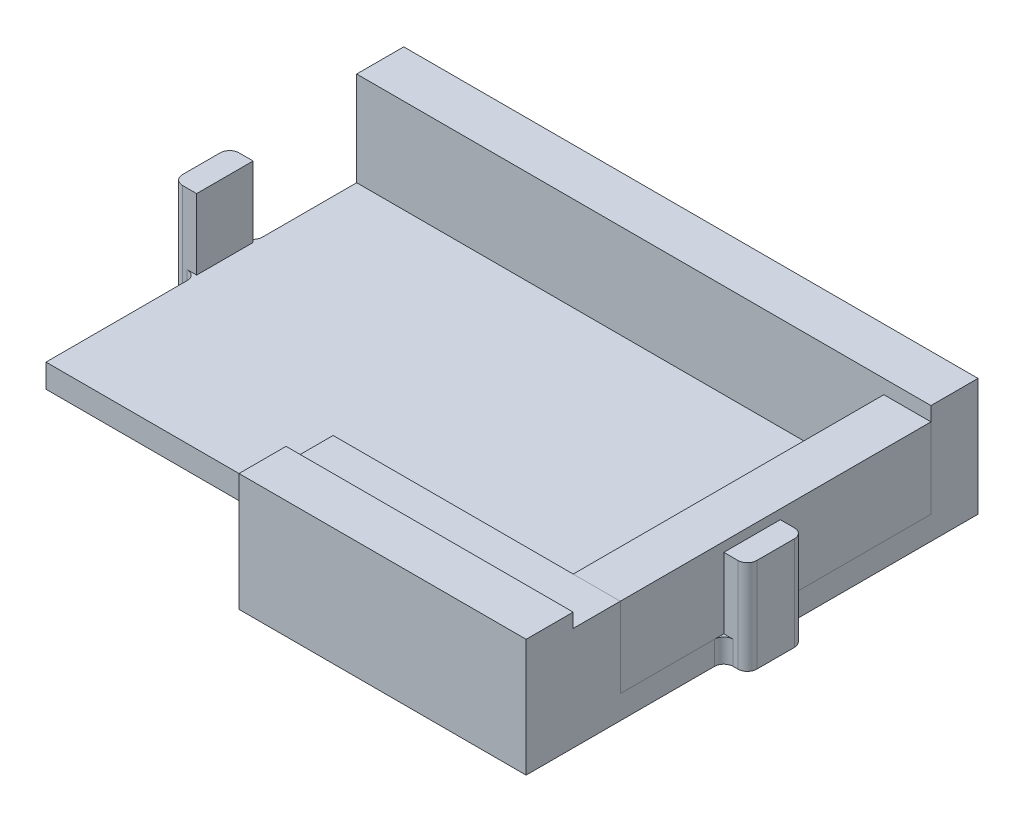
SolidWorks part; units mm, degrees
ref_plane "Front Plane" through (0, 0, 0) normal (0, 0, 1) x (1, 0, 0)
ref_plane "Top Plane" through (0, 0, 0) normal (0, 1, 0) x (1, 0, 0)
ref_plane "Right Plane" through (0, 0, 0) normal (1, 0, 0) x (0, 0, -1)
sketch "Sketch1" plane through (0, 0, 0) normal (0, 1, 0) x (1, 0, 0)
  line L0 (0, 10) -> (30.5, 10)
  line L3 (0, 48) -> (61, 48)
  line L4 (61, 0) -> (61, 48)
  line L5 (30.5, 10) -> (30.5, 0)
  line L6 (0, 48) -> (0, 10)
  line L7 (30.5, 0) -> (61, 0)
  dimension "D1" = 61
  dimension "D2" = 48
  dimension "D3" = 30.5
  dimension "D4" = 10
extrude "Boss-Extrude1" add sketch "Sketch1" along normal blind 2.5
sketch "Sketch2" plane through (0, 2.5, 0) normal (0, 1, 0) x (1, 0, 0)
  line L24 (61, 0) -> (61, 48) construction
  line L25 (0, 48) -> (61, 48)
  line L26 (0, 48) -> (0, 43)
  line L27 (0, 43) -> (61, 43)
  line L28 (61, 48) -> (61, 43)
  line L30 (30.5, 0) -> (61, 0)
  line L31 (30.5, 0) -> (30.5, 5)
  line L32 (30.5, 5) -> (61, 5)
  line L33 (61, 0) -> (61, 5)
  dimension "D1" = 5
  dimension "D2" = 5
extrude "Boss-Extrude2" add sketch "Sketch2" along normal blind 10
sketch "Sketch3" plane through (0, 0, 0) normal (0, -1, 0) x (1, 0, 0)
  line L0 (61, -24) -> (0, -24) construction
  line L1 (61, 0) -> (61, -48) construction
  line L2 (0, -48) -> (0, -10) construction
  text T0 "PCB" font "Arial Rounded MT Bold" height 8
extrude "Cut-Extrude1" cut sketch "Sketch3" against normal blind 1
sketch "Sketch5" plane through (0, 0, 0) normal (0, -1, 0) x (1, 0, 0)
  line L0 (0, -29) -> (61, -29) construction
  line L1 (0, -48) -> (0, -10) construction
  line L2 (61, 0) -> (61, -48) construction
  line L3 (0, -26) -> (61, -26) construction
  line L4 (0, -32) -> (61, -32) construction
  line L7 (61, -24) -> (0, -24) construction
  line L8 (61, -21) -> (33.7768, -21) construction
  line L9 (61, -27) -> (35.9613, -27) construction
  line L12 (0, -26) -> (-2.5, -26)
  line L13 (0, -26) -> (0, -32)
  line L14 (0, -32) -> (-2.5, -32)
  line L15 (-2.5, -26) -> (-2.5, -32)
  line L16 (61, -21) -> (63.5, -21)
  line L17 (61, -21) -> (61, -27)
  line L18 (61, -27) -> (63.5, -27)
  line L19 (63.5, -21) -> (63.5, -27)
  dimension "D1" = 3
  dimension "D2" = 3
  dimension "D3" = 3
  dimension "D4" = 3
  dimension "D5" = 2.5
  dimension "D6" = 2.5
extrude "Boss-Extrude3" add sketch "Sketch5" against normal blind 10
fillet "Fillet4" radius 1 8 edges at (0, 1.25, -26) (0, 1.25, -32) (-2.5, 5, -32) (-2.5, 5, -26) (61, 1.25, -27) (61, 1.25, -21) (63.5, 5, -21) (63.5, 5, -27)
sketch "Sketch6" plane through (0, 2.5, 0) normal (0, 1, 0) x (1, 0, 0)
  line L1 (30.5, 10) -> (61, 10)
  line L2 (30.5, 10) -> (30.5, 5)
  line L3 (30.5, 5) -> (61, 5)
  line L4 (61, 10) -> (61, 5)
extrude "Boss-Extrude4" add sketch "Sketch6" along normal blind 8.5
sketch "Sketch7" plane through (0, 2.5, 0) normal (0, 1, 0) x (1, 0, 0)
  line L0 (0, 43) -> (61, 43) construction
  line L1 (61, 10) -> (56, 10)
  line L2 (61, 10) -> (61, 43)
  line L3 (61, 43) -> (56, 43)
  line L4 (56, 10) -> (56, 43)
  dimension "D1" = 5
extrude "Boss-Extrude5" add sketch "Sketch7" along normal blind 8.5 separate body
